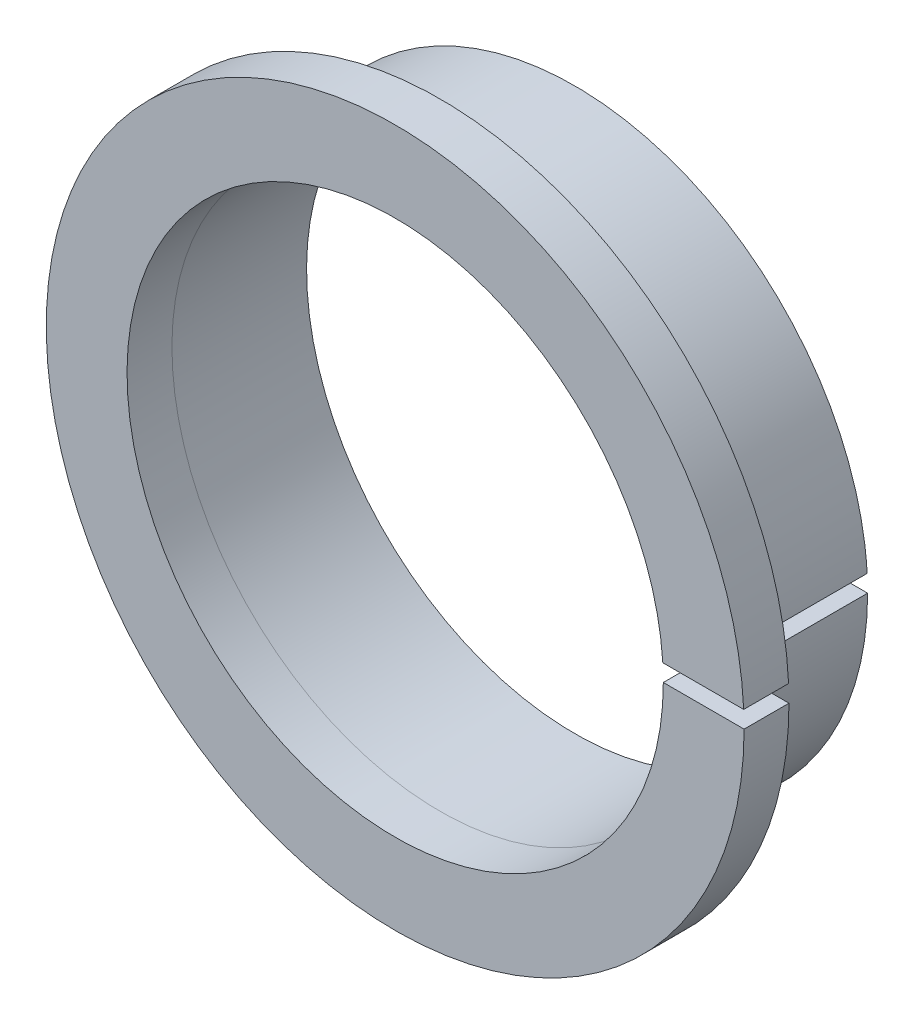
SolidWorks part; units mm, degrees
ref_plane "Front Plane" through (0, 0, 0) normal (0, 0, 1) x (1, 0, 0)
ref_plane "Top Plane" through (0, 0, 0) normal (0, 1, 0) x (1, 0, 0)
ref_plane "Right Plane" through (0, 0, 0) normal (1, 0, 0) x (0, 0, -1)
sketch "Sketch1" plane through (0, 0, 0) normal (0, 0, 1) x (1, 0, 0)
  line L6 (11.9258, 0.75) -> (15.5311, 0.7501)
  line L7 (15.5492, 0) -> (11.9494, 0)
  arc A2 (11.9258, 0.75) -> (11.9494, 0) centre (0, 0) ccw
  arc A3 (15.5311, 0.7501) -> (15.5492, 0) centre (0, 0) ccw
  dimension "D1" = 11.9494
  dimension "D2" = 15.5492
  dimension "D3" = 3.5998
  dimension "D4" = 3.6053
extrude "Boss-Extrude1" add sketch "Sketch1" against normal blind 2 separate body
sketch "Sketch2" plane through (0, 0, -2) normal (0, 0, -1) x (-1, 0, 0)
  line L0 (-13.0543, 0) -> (-11.9494, 0)
  line L1 (-13.0328, 0.7501) -> (-11.9258, 0.75)
  arc A1 (-11.9494, 0) -> (-11.9258, 0.75) centre (0, 0) ccw
  ellipse E1 centre (0, 0) end of major axis (0, 13.0543) minor radius 13.0543 (-13.0543, 0) -> (-13.0328, 0.7501) ccw
extrude "Boss-Extrude2" add sketch "Sketch2" along normal blind 6
